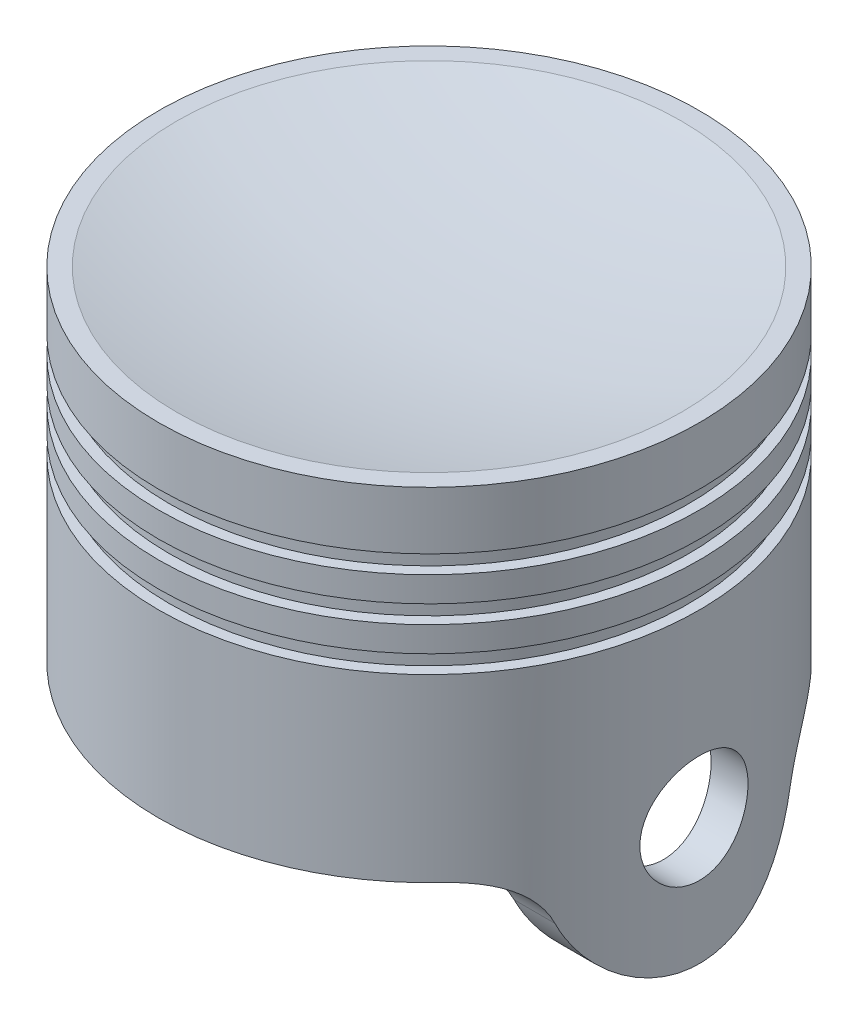
SolidWorks part; units mm, degrees
ref_plane "Front" through (0, 0, 0) normal (0, 0, 1) x (1, 0, 0)
ref_plane "Top" through (0, 0, 0) normal (0, 1, 0) x (1, 0, 0)
ref_plane "Right" through (0, 0, 0) normal (1, 0, 0) x (0, 0, -1)
sketch "Sketch1" plane through (0, 0, 0) normal (1, 0, 0) x (0, 0, -1)
  line L0 (-32.5, -37.5) -> (-32.5, 17.5)
  line L1 (37.5, -37.5) -> (-37.5, -37.5)
  line L2 (37.5, -37.5) -> (37.5, 37.5)
  line L3 (37.5, 37.5) -> (-37.5, 37.5)
  line L4 (-37.5, -37.5) -> (-37.5, 37.5)
  line L5 (37.5, -37.5) -> (-37.5, 37.5) construction
  line L6 (37.5, 37.5) -> (-37.5, -37.5) construction
  line L7 (-32.5, 17.5) -> (32.5, 17.5)
  line L8 (32.5, 17.5) -> (32.5, -37.5)
  line L9 (0, 37.5) -> (0, -14.7504)
  line L10 (-37.5, 29.5) -> (-36, 29.5)
  line L11 (-36, 29.5) -> (-36, 27)
  line L12 (-36, 27) -> (-37.5, 27)
  line L13 (-36, 21) -> (-37.5, 21)
  line L14 (-36, 23.5) -> (-36, 21)
  line L15 (-37.5, 23.5) -> (-36, 23.5)
  line L16 (-36, 15) -> (-37.5, 15)
  line L17 (-36, 17.5) -> (-36, 15)
  line L18 (-37.5, 17.5) -> (-36, 17.5)
  arc A0 (-35, 37.5) -> (35, 37.5) centre (0, 171.3611) ccw
  point P0 (0, 0)
  point P15 (0, 33)
  dimension "D6" = 2.5
  dimension "D1" = 75
  dimension "D2" = 75
  dimension "D3" = 5
  dimension "D4" = 5
  dimension "D5" = 20
  dimension "D7" = 2.5
  dimension "D8" = 4.5
  dimension "D9" = 1.5
  dimension "D10" = 2.5
  dimension "D11" = 8
  dimension "D12" = 3
revolve "Revolve1" add sketch "Sketch1" angle 360 about L9
sketch "Sketch2" plane through (0, 0, 0) normal (1, 0, 0) x (0, 0, -1)
  circle A0 centre (0, -10) radius 7.5
  dimension "D1" = 15
  dimension "D2" = 10
extrude "Cut-Extrude1" cut sketch "Sketch2" against normal through all both and the other way through all
sketch "Sketch3" plane through (0, 0, 0) normal (1, 0, 0) x (0, 0, -1)
  line L0 (54.2986, -10) -> (-54.2986, -10)
  line L1 (0, -10) -> (0, -5.2647) construction
  line L2 (54.2986, -10) -> (55.2014, -46.4595)
  line L3 (55.2014, -46.4595) -> (-43.0797, -45.071)
  line L4 (-43.0797, -45.071) -> (-54.2986, -10)
  circle A0 centre (0, -10) radius 17.5
  arc A1 (-25.6174, -10) -> (-16.302, -16.3636) centre (-25.6174, -20) cw
  arc A2 (25.6174, -10) -> (16.302, -16.3636) centre (25.6174, -20) ccw
  point P6 (0, -10)
  dimension "D1" = 35
  dimension "D2" = 10
extrude "Cut-Extrude2" cut sketch "Sketch3" against normal through all both and the other way through all contours L0 A2 A0 A1 L4 L3 L2
